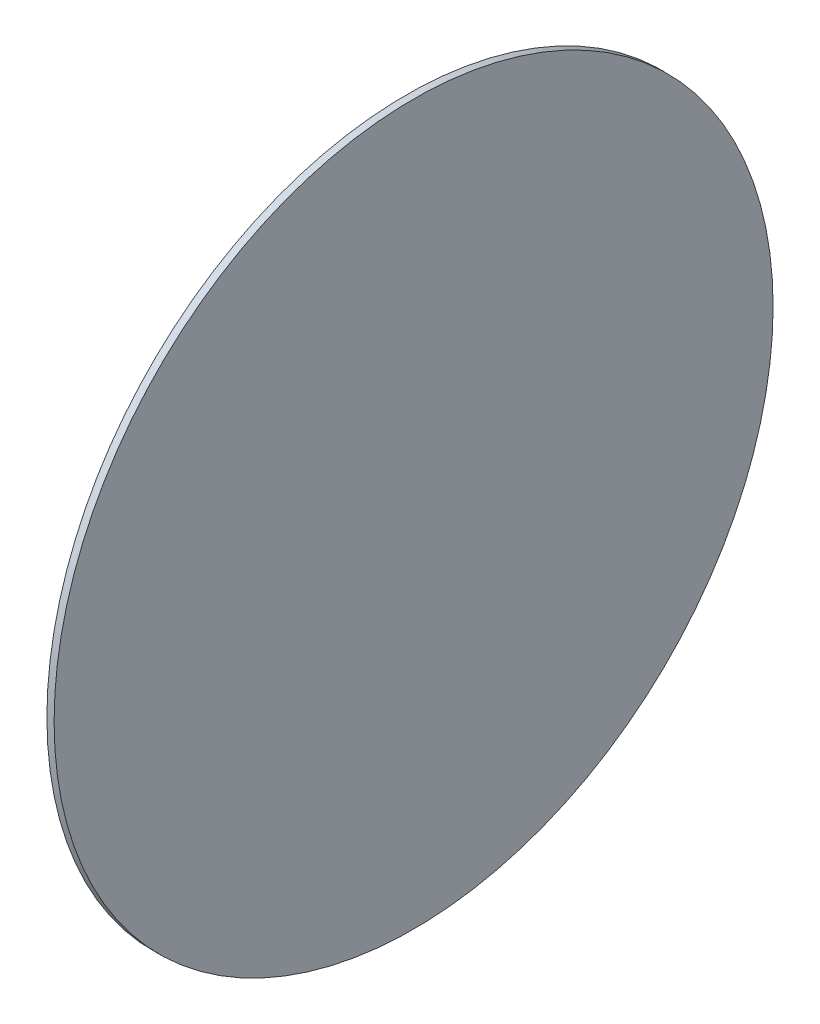
SolidWorks part; units mm, degrees
ref_plane "Front Plane" through (0, 0, 0) normal (0, 0, 1) x (1, 0, 0)
ref_plane "Top Plane" through (0, 0, 0) normal (0, 1, 0) x (1, 0, 0)
ref_plane "Right Plane" through (0, 0, 0) normal (1, 0, 0) x (0, 0, -1)
sketch "Sketch1" plane through (0, 0, 0) normal (1, 0, 0) x (0, 0, -1)
  circle A0 centre (0, 0) radius 150
  dimension "D1" = 300
sketch "Sketch2" plane through (0, 0, 0) normal (1, 0, 0) x (0, 0, -1)
  circle A0 centre (0, 0) radius 150 construction
  circle A1 centre (0, 0) radius 150
extrude "Boss-Extrude1" add sketch "Sketch2" along normal blind 3
